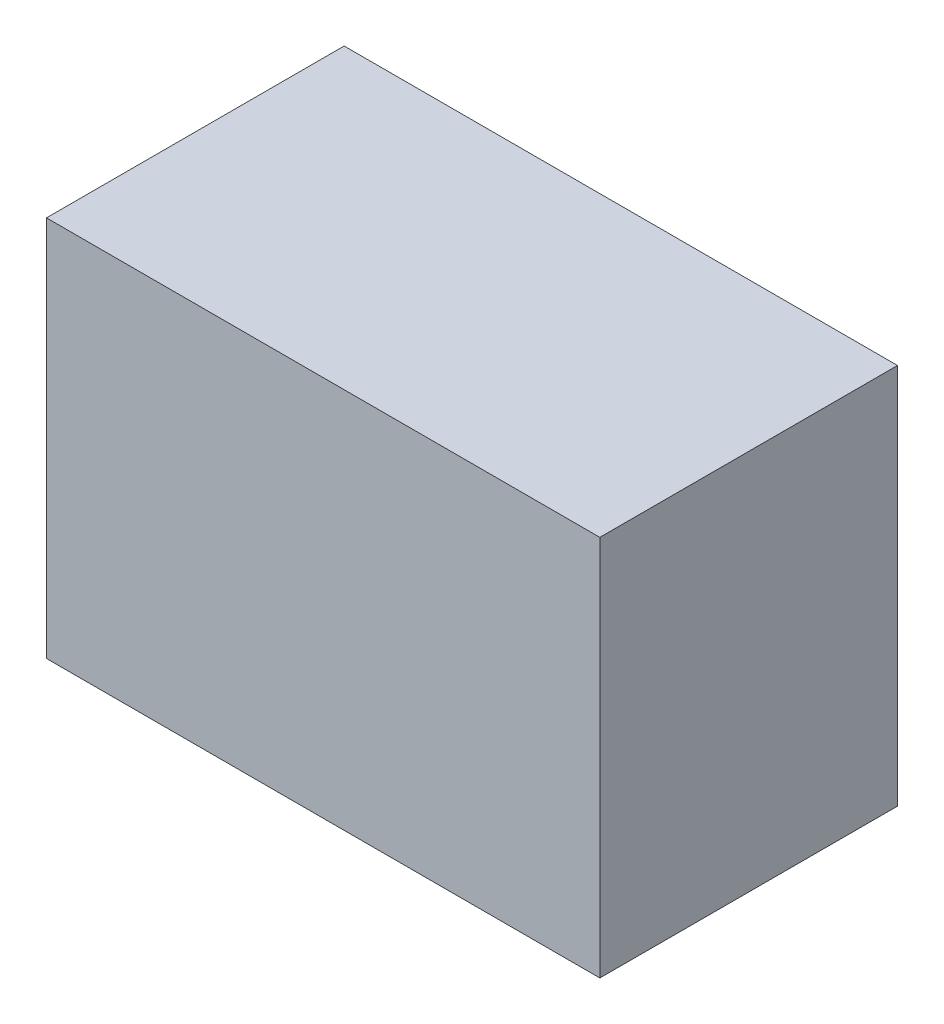
SolidWorks part; units mm, degrees
material "Pine"
ref_plane "Front Plane" through (0, 0, 0) normal (0, 0, 1) x (1, 0, 0)
ref_plane "Top Plane" through (0, 0, 0) normal (0, 1, 0) x (1, 0, 0)
ref_plane "Right Plane" through (0, 0, 0) normal (1, 0, 0) x (0, 0, -1)
sketch "Sketch1" plane through (0, 0, 0) normal (0, 0, 1) x (1, 0, 0)
  line L1 (600, 72.5) -> (455, 72.5)
  line L2 (600, 72.5) -> (600, -27.5)
  line L3 (600, -27.5) -> (455, -27.5)
  line L4 (455, 72.5) -> (455, -27.5)
  dimension "D1" = 100
  dimension "D2" = 145
extrude "Boss-Extrude1" add sketch "Sketch1" along normal blind 78
